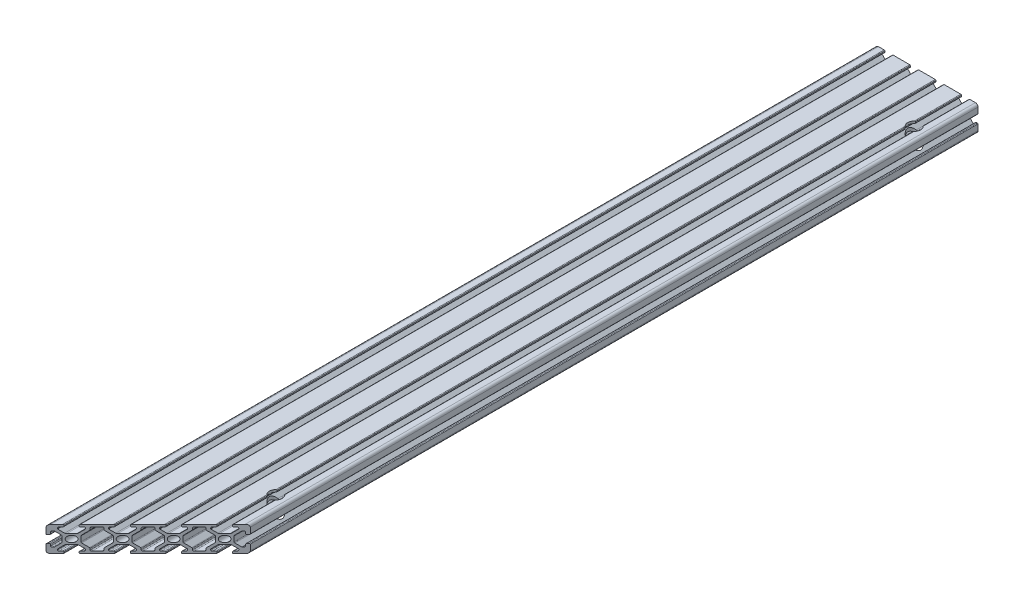
SolidWorks part; units mm, degrees
material "6063-T5"
ref_plane "Front Plane" through (0, 0, 0) normal (0, 0, 1) x (1, 0, 0)
ref_plane "Top Plane" through (0, 0, 0) normal (0, 1, 0) x (1, 0, 0)
ref_plane "Right Plane" through (0, 0, 0) normal (1, 0, 0) x (0, 0, -1)
sketch "Sketch1" plane through (0, 0, 0) normal (0, 0, 1) x (1, 0, 0)
  line L0 (2, 0) -> (6.5, 0)
  line L1 (80, 2) -> (80, 6.5)
  line L2 (78, 20) -> (73.5, 20)
  line L3 (0, 18) -> (0, 13.5)
  line L4 (33, 19.5) -> (33, 18.7)
  line L5 (27, 19.5) -> (27, 18.7)
  line L6 (7, 19.5) -> (7, 18.7)
  line L7 (13, 19.5) -> (13, 18.7)
  line L8 (6.5, 20) -> (2, 20)
  line L9 (53, 19.5) -> (53, 18.7)
  line L10 (47, 19.5) -> (47, 18.7)
  line L11 (73, 19.5) -> (73, 18.7)
  line L12 (67, 19.5) -> (67, 18.7)
  line L13 (33, 1.3) -> (33, 0.5)
  line L14 (27, 1.3) -> (27, 0.5)
  line L15 (53, 1.3) -> (53, 0.5)
  line L16 (47, 1.3) -> (47, 0.5)
  line L17 (73, 1.3) -> (73, 0.5)
  line L18 (67, 1.3) -> (67, 0.5)
  line L19 (13, 1.3) -> (13, 0.5)
  line L20 (7, 1.3) -> (7, 0.5)
  line L21 (13.5, 20) -> (26.5, 20) construction
  line L22 (26.5, 20) -> (13.5, 20)
  line L23 (46.5, 20) -> (33.5, 20)
  line L24 (66.5, 20) -> (53.5, 20)
  line L25 (73.5, 0) -> (78, 0)
  line L26 (53.5, 0) -> (66.5, 0)
  line L27 (33.5, 0) -> (46.5, 0)
  line L28 (13.5, 0) -> (26.5, 0)
  line L29 (79.5, 13) -> (78.7, 13)
  line L30 (79.5, 7) -> (78.7, 7)
  line L31 (0.5, 13) -> (1.3, 13)
  line L32 (0.5, 7) -> (1.3, 7)
  line L33 (0, 6.5) -> (0, 2)
  line L34 (80, 13.5) -> (80, 18)
  line L35 (1.8, 13.5) -> (1.8, 14.75)
  line L36 (5.25, 18.2) -> (6.5, 18.2)
  line L37 (78.2, 14.75) -> (78.2, 13.5)
  line L38 (74.75, 1.8) -> (73.5, 1.8)
  line L39 (1.8, 5.25) -> (1.8, 6.5)
  line L40 (13.5, 18.2) -> (14.75, 18.2)
  line L41 (6.5, 1.8) -> (5.25, 1.8)
  line L42 (33.5, 18.2) -> (34.75, 18.2)
  line L43 (26.5, 1.8) -> (25.25, 1.8)
  line L44 (53.5, 18.2) -> (54.75, 18.2)
  line L45 (46.5, 1.8) -> (45.25, 1.8)
  line L46 (73.5, 18.2) -> (74.75, 18.2)
  line L47 (66.5, 1.8) -> (65.25, 1.8)
  line L48 (78.2, 6.5) -> (78.2, 5.25)
  line L49 (12.6701, 13.9429) -> (15.5, 16.7728)
  line L50 (12.6701, 6.0571) -> (15.5, 3.2272)
  line L51 (32.6701, 13.9429) -> (35.5, 16.7728)
  line L52 (33.9429, 12.6701) -> (37.0803, 15.8075)
  line L53 (27.3299, 13.9429) -> (24.5, 16.7728)
  line L54 (22.9197, 15.8075) -> (26.0571, 12.6701)
  line L55 (27.3299, 6.0571) -> (24.5, 3.2272)
  line L56 (22.9197, 4.1925) -> (26.0571, 7.3299)
  line L57 (47.3299, 13.9429) -> (44.5, 16.7728)
  line L58 (42.9197, 15.8075) -> (46.0571, 12.6701)
  line L59 (47.3299, 6.0571) -> (44.5, 3.2272)
  line L60 (42.9197, 4.1925) -> (46.0571, 7.3299)
  line L61 (67.3299, 13.9429) -> (64.5, 16.7728)
  line L62 (62.9197, 15.8075) -> (66.0571, 12.6701)
  line L63 (67.3299, 6.0571) -> (64.5, 3.2272)
  line L64 (62.9197, 4.1925) -> (66.0571, 7.3299)
  line L65 (33.9429, 7.3299) -> (37.0803, 4.1925)
  line L66 (13.9429, 12.6701) -> (17.0803, 15.8075)
  line L67 (6.0571, 7.3299) -> (3.2272, 4.5)
  line L68 (7.3299, 6.0571) -> (4.5, 3.2272)
  line L69 (7.3299, 13.9429) -> (4.5, 16.7728)
  line L70 (32.6701, 6.0571) -> (35.5, 3.2272)
  line L71 (13.9429, 7.3299) -> (17.0803, 4.1925)
  line L72 (52.6701, 13.9429) -> (55.5, 16.7728)
  line L73 (6.0571, 12.6701) -> (3.2272, 15.5)
  line L74 (53.9429, 12.6701) -> (57.0803, 15.8075)
  line L75 (53.9429, 7.3299) -> (57.0803, 4.1925)
  line L76 (52.6701, 6.0571) -> (55.5, 3.2272)
  line L77 (72.6701, 13.9429) -> (75.5, 16.7728)
  line L78 (73.9429, 12.6701) -> (76.7728, 15.5)
  line L79 (73.9429, 7.3299) -> (76.7728, 4.5)
  line L80 (72.6701, 6.0571) -> (75.5, 3.2272)
  line L81 (28.037, 13.65) -> (31.963, 13.65)
  line L82 (18.05, 18.2) -> (21.95, 18.2)
  line L83 (14.75, 1.8) -> (13.5, 1.8)
  line L84 (15.5, 17.45) -> (15.5, 16.7728)
  line L85 (34.75, 1.8) -> (33.5, 1.8)
  line L86 (4.5, 17.45) -> (4.5, 16.7728)
  line L87 (54.75, 1.8) -> (53.5, 1.8)
  line L88 (24.5, 17.45) -> (24.5, 16.7728)
  line L89 (27.7144, 8.9872) -> (21.8, 3.0728) [skipped]
  line L90 (25.25, 18.2) -> (26.5, 18.2)
  line L91 (27.7144, 11.0128) -> (21.8, 16.9272) [skipped]
  line L92 (45.25, 18.2) -> (46.5, 18.2)
  line L93 (33.65, 11.963) -> (33.65, 8.037)
  line L94 (31.963, 6.35) -> (28.037, 6.35)
  line L95 (26.35, 8.037) -> (26.35, 11.963)
  line L96 (65.25, 18.2) -> (66.5, 18.2)
  line L97 (44.5, 17.45) -> (44.5, 16.7728)
  line L98 (35.5, 17.45) -> (35.5, 16.7728)
  line L99 (47.7144, 8.9872) -> (41.8, 3.0728) [skipped]
  line L100 (47.7144, 11.0128) -> (41.8, 16.9272) [skipped]
  line L101 (67.7144, 11.0128) -> (61.8, 16.9272) [skipped]
  line L102 (67.7144, 8.9872) -> (61.8, 3.0728) [skipped]
  line L103 (13.65, 11.963) -> (13.65, 8.037)
  line L104 (11.963, 6.35) -> (8.037, 6.35)
  line L105 (6.35, 8.037) -> (6.35, 11.963)
  line L106 (8.037, 13.65) -> (11.963, 13.65)
  line L107 (48.037, 13.65) -> (51.963, 13.65)
  line L108 (53.65, 11.963) -> (53.65, 8.037)
  line L109 (51.963, 6.35) -> (48.037, 6.35)
  line L110 (46.35, 8.037) -> (46.35, 11.963)
  line L111 (68.037, 13.65) -> (71.963, 13.65)
  line L112 (73.65, 11.963) -> (73.65, 8.037)
  line L113 (71.963, 6.35) -> (68.037, 6.35)
  line L114 (66.35, 8.037) -> (66.35, 11.963)
  line L115 (64.5, 17.45) -> (64.5, 16.7728)
  line L116 (55.5, 17.45) -> (55.5, 16.7728)
  line L117 (4.5, 2.55) -> (4.5, 3.2272)
  line L118 (75.5, 17.45) -> (75.5, 16.7728)
  line L119 (24.5, 2.55) -> (24.5, 3.2272)
  line L120 (15.5, 2.55) -> (15.5, 3.2272)
  line L121 (44.5, 2.55) -> (44.5, 3.2272)
  line L122 (35.5, 2.55) -> (35.5, 3.2272)
  line L123 (64.5, 2.55) -> (64.5, 3.2272)
  line L124 (55.5, 2.55) -> (55.5, 3.2272)
  line L125 (2.55, 15.5) -> (3.2272, 15.5)
  line L126 (75.5, 2.55) -> (75.5, 3.2272)
  line L127 (2.55, 4.5) -> (3.2272, 4.5)
  line L128 (77.45, 15.5) -> (76.7728, 15.5)
  line L129 (17.3, 17.45) -> (17.3, 16.3379)
  line L130 (77.45, 4.5) -> (76.7728, 4.5)
  line L131 (22.7, 17.45) -> (22.7, 16.3379)
  line L132 (38.05, 18.2) -> (41.95, 18.2)
  line L133 (37.3, 17.45) -> (37.3, 16.3379)
  line L134 (42.7, 17.45) -> (42.7, 16.3379)
  line L135 (58.05, 18.2) -> (61.95, 18.2)
  line L136 (57.3, 17.45) -> (57.3, 16.3379)
  line L137 (62.7, 17.45) -> (62.7, 16.3379)
  line L138 (17.3, 3.6621) -> (17.3, 2.55)
  line L139 (18.05, 1.8) -> (21.95, 1.8)
  line L140 (22.7, 2.55) -> (22.7, 3.6621)
  line L141 (37.3, 3.6621) -> (37.3, 2.55)
  line L142 (38.05, 1.8) -> (41.95, 1.8)
  line L143 (42.7, 2.55) -> (42.7, 3.6621)
  line L144 (57.3, 3.6621) -> (57.3, 2.55)
  line L145 (58.05, 1.8) -> (61.95, 1.8)
  line L146 (62.7, 2.55) -> (62.7, 3.6621)
  circle A0 centre (10, 10) radius 2.5
  circle A1 centre (30, 10) radius 2.5
  circle A2 centre (50, 10) radius 2.5
  circle A3 centre (70, 10) radius 2.5
  arc A4 (78, 0) -> (80, 2) centre (78, 2) ccw
  arc A5 (80, 18) -> (78, 20) centre (78, 18) ccw
  arc A6 (2, 0) -> (0, 2) centre (2, 2) cw
  arc A7 (2, 20) -> (0, 18) centre (2, 18) ccw
  arc A8 (12.6701, 13.9429) -> (11.963, 13.65) centre (11.963, 14.65) cw
  arc A9 (7.3299, 13.9429) -> (8.037, 13.65) centre (8.037, 14.65) ccw
  arc A10 (6.0571, 12.6701) -> (6.35, 11.963) centre (5.35, 11.963) cw
  arc A11 (6.0571, 7.3299) -> (6.35, 8.037) centre (5.35, 8.037) ccw
  arc A12 (7.3299, 6.0571) -> (8.037, 6.35) centre (8.037, 5.35) cw
  arc A13 (12.6701, 6.0571) -> (11.963, 6.35) centre (11.963, 5.35) ccw
  arc A14 (32.6701, 6.0571) -> (31.963, 6.35) centre (31.963, 5.35) ccw
  arc A15 (27.3299, 6.0571) -> (28.037, 6.35) centre (28.037, 5.35) cw
  arc A16 (27.3299, 13.9429) -> (28.037, 13.65) centre (28.037, 14.65) ccw
  arc A17 (32.6701, 13.9429) -> (31.963, 13.65) centre (31.963, 14.65) cw
  arc A18 (47.3299, 6.0571) -> (48.037, 6.35) centre (48.037, 5.35) cw
  arc A19 (52.6701, 6.0571) -> (51.963, 6.35) centre (51.963, 5.35) ccw
  arc A20 (52.6701, 13.9429) -> (51.963, 13.65) centre (51.963, 14.65) cw
  arc A21 (47.3299, 13.9429) -> (48.037, 13.65) centre (48.037, 14.65) ccw
  arc A22 (72.6701, 13.9429) -> (71.963, 13.65) centre (71.963, 14.65) cw
  arc A23 (67.3299, 13.9429) -> (68.037, 13.65) centre (68.037, 14.65) ccw
  arc A24 (67.3299, 6.0571) -> (68.037, 6.35) centre (68.037, 5.35) cw
  arc A25 (72.6701, 6.0571) -> (71.963, 6.35) centre (71.963, 5.35) ccw
  arc A26 (73.9429, 7.3299) -> (73.65, 8.037) centre (74.65, 8.037) cw
  arc A27 (73.9429, 12.6701) -> (73.65, 11.963) centre (74.65, 11.963) ccw
  arc A28 (66.0571, 7.3299) -> (66.35, 8.037) centre (65.35, 8.037) ccw
  arc A29 (66.0571, 12.6701) -> (66.35, 11.963) centre (65.35, 11.963) cw
  arc A30 (53.9429, 7.3299) -> (53.65, 8.037) centre (54.65, 8.037) cw
  arc A31 (53.9429, 12.6701) -> (53.65, 11.963) centre (54.65, 11.963) ccw
  arc A32 (78.2, 14.75) -> (77.45, 15.5) centre (77.45, 14.75) ccw
  arc A33 (75.5, 17.45) -> (74.75, 18.2) centre (74.75, 17.45) ccw
  arc A34 (78.2, 5.25) -> (77.45, 4.5) centre (77.45, 5.25) cw
  arc A35 (75.5, 2.55) -> (74.75, 1.8) centre (74.75, 2.55) cw
  arc A36 (46.0571, 7.3299) -> (46.35, 8.037) centre (45.35, 8.037) ccw
  arc A37 (46.0571, 12.6701) -> (46.35, 11.963) centre (45.35, 11.963) cw
  arc A38 (33.9429, 7.3299) -> (33.65, 8.037) centre (34.65, 8.037) cw
  arc A39 (33.9429, 12.6701) -> (33.65, 11.963) centre (34.65, 11.963) ccw
  arc A40 (13.9429, 12.6701) -> (13.65, 11.963) centre (14.65, 11.963) ccw
  arc A41 (13.9429, 7.3299) -> (13.65, 8.037) centre (14.65, 8.037) cw
  arc A42 (26.0571, 7.3299) -> (26.35, 8.037) centre (25.35, 8.037) ccw
  arc A43 (26.0571, 12.6701) -> (26.35, 11.963) centre (25.35, 11.963) cw
  arc A44 (65.25, 1.8) -> (64.5, 2.55) centre (65.25, 2.55) cw
  arc A45 (61.95, 1.8) -> (62.7, 2.55) centre (61.95, 2.55) ccw
  arc A46 (57.3, 2.55) -> (58.05, 1.8) centre (58.05, 2.55) ccw
  arc A47 (54.75, 1.8) -> (55.5, 2.55) centre (54.75, 2.55) ccw
  arc A48 (45.25, 1.8) -> (44.5, 2.55) centre (45.25, 2.55) cw
  arc A49 (64.5, 17.45) -> (65.25, 18.2) centre (65.25, 17.45) cw
  arc A50 (61.95, 18.2) -> (62.7, 17.45) centre (61.95, 17.45) cw
  arc A51 (58.05, 18.2) -> (57.3, 17.45) centre (58.05, 17.45) ccw
  arc A52 (53, 18.7) -> (53.5, 18.2) centre (53.5, 18.7) ccw
  arc A53 (53, 19.5) -> (53.5, 20) centre (53.5, 19.5) cw
  arc A54 (67, 18.7) -> (66.5, 18.2) centre (66.5, 18.7) cw
  arc A55 (67, 19.5) -> (66.5, 20) centre (66.5, 19.5) ccw
  arc A56 (73, 18.7) -> (73.5, 18.2) centre (73.5, 18.7) ccw
  arc A57 (73, 19.5) -> (73.5, 20) centre (73.5, 19.5) cw
  arc A58 (78.7, 13) -> (78.2, 13.5) centre (78.7, 13.5) cw
  arc A59 (79.5, 13) -> (80, 13.5) centre (79.5, 13.5) ccw
  arc A60 (78.7, 7) -> (78.2, 6.5) centre (78.7, 6.5) ccw
  arc A61 (79.5, 7) -> (80, 6.5) centre (79.5, 6.5) cw
  arc A62 (73, 0.5) -> (73.5, 0) centre (73.5, 0.5) ccw
  arc A63 (73, 1.3) -> (73.5, 1.8) centre (73.5, 1.3) cw
  arc A64 (67, 0.5) -> (66.5, 0) centre (66.5, 0.5) cw
  arc A65 (67, 1.3) -> (66.5, 1.8) centre (66.5, 1.3) ccw
  arc A66 (53, 0.5) -> (53.5, 0) centre (53.5, 0.5) ccw
  arc A67 (53, 1.3) -> (53.5, 1.8) centre (53.5, 1.3) cw
  arc A68 (47, 0.5) -> (46.5, 0) centre (46.5, 0.5) cw
  arc A69 (47, 1.3) -> (46.5, 1.8) centre (46.5, 1.3) ccw
  arc A70 (33, 0.5) -> (33.5, 0) centre (33.5, 0.5) ccw
  arc A71 (33, 1.3) -> (33.5, 1.8) centre (33.5, 1.3) cw
  arc A72 (27, 0.5) -> (26.5, 0) centre (26.5, 0.5) cw
  arc A73 (27, 1.3) -> (26.5, 1.8) centre (26.5, 1.3) ccw
  arc A74 (47, 18.7) -> (46.5, 18.2) centre (46.5, 18.7) cw
  arc A75 (47, 19.5) -> (46.5, 20) centre (46.5, 19.5) ccw
  arc A76 (33, 18.7) -> (33.5, 18.2) centre (33.5, 18.7) ccw
  arc A77 (33, 19.5) -> (33.5, 20) centre (33.5, 19.5) cw
  arc A78 (27, 18.7) -> (26.5, 18.2) centre (26.5, 18.7) cw
  arc A79 (27, 19.5) -> (26.5, 20) centre (26.5, 19.5) ccw
  arc A80 (13, 18.7) -> (13.5, 18.2) centre (13.5, 18.7) ccw
  arc A81 (13.5, 20) -> (13, 19.5) centre (13.5, 19.5) ccw
  arc A82 (13, 0.5) -> (13.5, 0) centre (13.5, 0.5) ccw
  arc A83 (13, 1.3) -> (13.5, 1.8) centre (13.5, 1.3) cw
  arc A84 (7, 0.5) -> (6.5, 0) centre (6.5, 0.5) cw
  arc A85 (7, 1.3) -> (6.5, 1.8) centre (6.5, 1.3) ccw
  arc A86 (0, 6.5) -> (0.5, 7) centre (0.5, 6.5) cw
  arc A87 (1.3, 7) -> (1.8, 6.5) centre (1.3, 6.5) cw
  arc A88 (0, 13.5) -> (0.5, 13) centre (0.5, 13.5) ccw
  arc A89 (1.3, 13) -> (1.8, 13.5) centre (1.3, 13.5) ccw
  arc A90 (6.5, 20) -> (7, 19.5) centre (6.5, 19.5) cw
  arc A91 (7, 18.7) -> (6.5, 18.2) centre (6.5, 18.7) cw
  arc A92 (55.5, 17.45) -> (54.75, 18.2) centre (54.75, 17.45) ccw
  arc A93 (44.5, 17.45) -> (45.25, 18.2) centre (45.25, 17.45) cw
  arc A94 (37.3, 2.55) -> (38.05, 1.8) centre (38.05, 2.55) ccw
  arc A95 (38.05, 18.2) -> (37.3, 17.45) centre (38.05, 17.45) ccw
  arc A96 (41.95, 18.2) -> (42.7, 17.45) centre (41.95, 17.45) cw
  arc A97 (41.95, 1.8) -> (42.7, 2.55) centre (41.95, 2.55) ccw
  arc A98 (34.75, 1.8) -> (35.5, 2.55) centre (34.75, 2.55) ccw
  arc A99 (25.25, 1.8) -> (24.5, 2.55) centre (25.25, 2.55) cw
  arc A100 (14.75, 1.8) -> (15.5, 2.55) centre (14.75, 2.55) ccw
  arc A101 (5.25, 1.8) -> (4.5, 2.55) centre (5.25, 2.55) cw
  arc A102 (2.55, 4.5) -> (1.8, 5.25) centre (2.55, 5.25) cw
  arc A103 (1.8, 14.75) -> (2.55, 15.5) centre (2.55, 14.75) cw
  arc A104 (24.5, 17.45) -> (25.25, 18.2) centre (25.25, 17.45) cw
  arc A105 (34.75, 18.2) -> (35.5, 17.45) centre (34.75, 17.45) cw
  arc A106 (21.95, 18.2) -> (22.7, 17.45) centre (21.95, 17.45) cw
  arc A107 (18.05, 18.2) -> (17.3, 17.45) centre (18.05, 17.45) ccw
  arc A108 (15.5, 17.45) -> (14.75, 18.2) centre (14.75, 17.45) ccw
  arc A109 (5.25, 18.2) -> (4.5, 17.45) centre (5.25, 17.45) ccw
  arc A110 (62.7, 3.6621) -> (62.9197, 4.1925) centre (63.45, 3.6621) cw
  arc A111 (57.3, 3.6621) -> (57.0803, 4.1925) centre (56.55, 3.6621) ccw
  arc A112 (62.7, 16.3379) -> (62.9197, 15.8075) centre (63.45, 16.3379) ccw
  arc A113 (57.3, 16.3379) -> (57.0803, 15.8075) centre (56.55, 16.3379) cw
  arc A114 (42.7, 3.6621) -> (42.9197, 4.1925) centre (43.45, 3.6621) cw
  arc A115 (37.3, 3.6621) -> (37.0803, 4.1925) centre (36.55, 3.6621) ccw
  arc A116 (42.7, 16.3379) -> (42.9197, 15.8075) centre (43.45, 16.3379) ccw
  arc A117 (37.3, 16.3379) -> (37.0803, 15.8075) centre (36.55, 16.3379) cw
  arc A118 (22.7, 16.3379) -> (22.9197, 15.8075) centre (23.45, 16.3379) ccw
  arc A119 (17.3, 16.3379) -> (17.0803, 15.8075) centre (16.55, 16.3379) cw
  arc A120 (17.3, 3.6621) -> (17.0803, 4.1925) centre (16.55, 3.6621) ccw
  arc A121 (22.7, 3.6621) -> (22.9197, 4.1925) centre (23.45, 3.6621) cw
  arc A122 (21.95, 1.8) -> (22.7, 2.55) centre (21.95, 2.55) ccw
  arc A123 (17.3, 2.55) -> (18.05, 1.8) centre (18.05, 2.55) ccw
  point P124 (0, 0)
  point P394 (17.3, 16.0272)
  dimension "D1" = 4
  dimension "D3" = 4
  dimension "D2" = 2
  dimension "D4" = 3
extrude "Boss-Extrude1" add sketch "Sketch1" along normal mid plane 650
sketch "Sketch2" plane through (0, 20, 0) normal (0, 1, 0) x (1, 0, 0)
  line L0 (0, -325) -> (80, -245)
  line L1 (80, -325) -> (80, 325) construction
  line L2 (80, -245) -> (80, -325)
  line L3 (80, -325) -> (0, -325)
  dimension "D1" = 45
extrude "Cut-Extrude1" cut sketch "Sketch2" against normal through all
sketch "Sketch4" plane through (0, 6.35, 0) normal (0, -1, 0) x (-1, 0, 0)
  line L0 (-70, 325) -> (-70, 285) construction
  line L1 (-68.037, 325) -> (-71.963, 325) construction
  line L2 (-70, 285) -> (-70, -215) construction
  circle A0 centre (-70, 285) radius 5
  circle A1 centre (-70, -215) radius 5
  dimension "D1" = 10
  dimension "D4" = 10
  dimension "D2" = 40
  dimension "D3" = 500
extrude "Cut-Extrude3" cut sketch "Sketch4" against normal through all both and the other way through all
